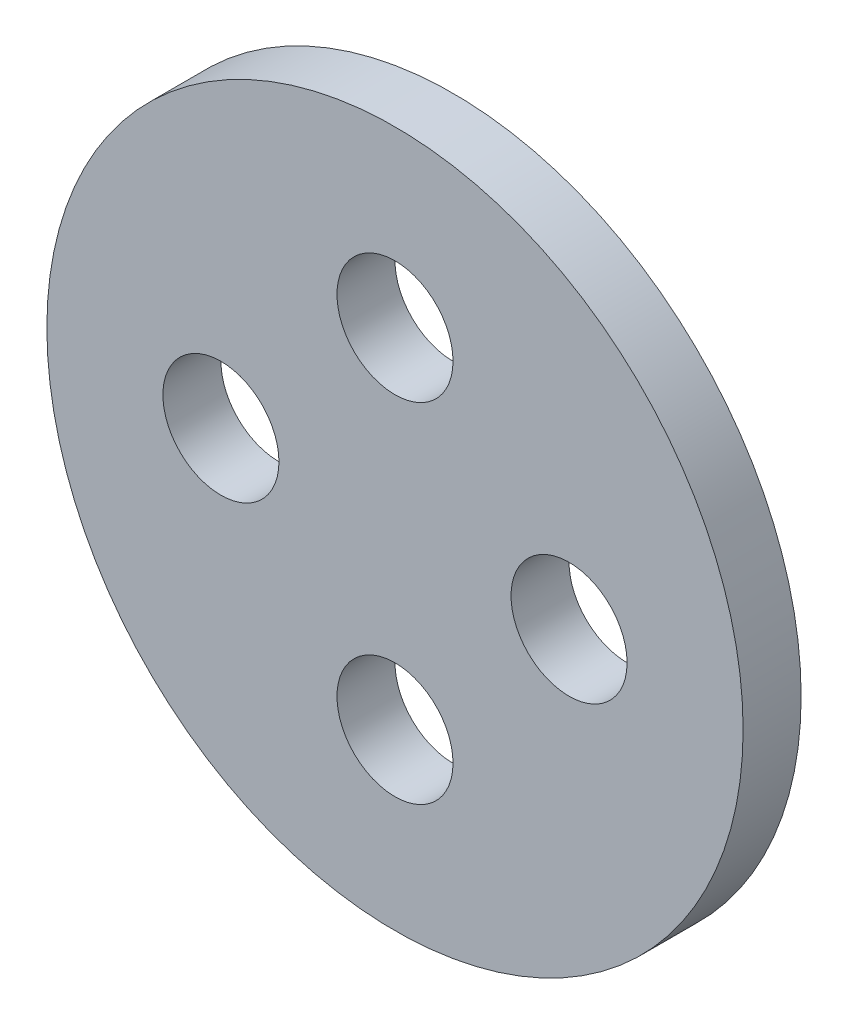
SolidWorks part; units mm, degrees
ref_plane "正面" through (0, 0, 0) normal (0, 0, 1) x (1, 0, 0)
ref_plane "平面" through (0, 0, 0) normal (0, 1, 0) x (1, 0, 0)
ref_plane "右側面" through (0, 0, 0) normal (1, 0, 0) x (0, 0, -1)
sketch "ｽｹｯﾁ1" plane through (0, 0, 0) normal (0, 0, 1) x (1, 0, 0)
  circle A0 centre (0, 0) radius 6
  circle A2 centre (0, 3) radius 1
  circle A3 centre (3, 0) radius 1
  circle A4 centre (0, -3) radius 1
  circle A5 centre (-3, 0) radius 1
  point P15 (0, 0)
  dimension "D1" = 12
  dimension "D3" = 2
  dimension "D4" = 3
  dimension "D5" = 4
extrude "ﾎﾞｽ - 押し出し1" add sketch "ｽｹｯﾁ1" along normal blind 1
